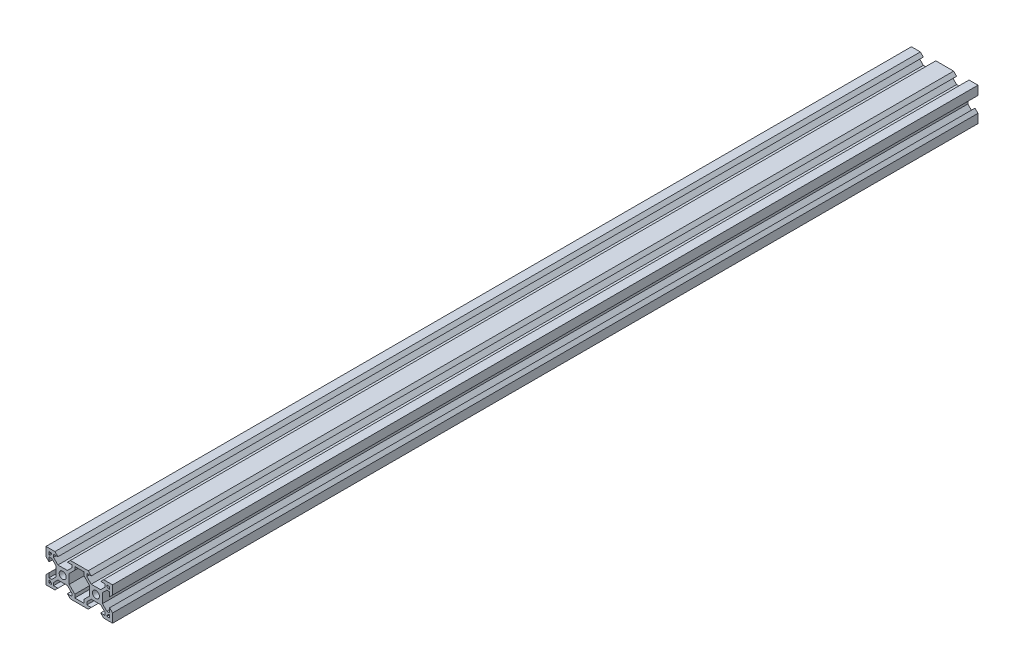
SolidWorks part; units mm, degrees
ref_plane "Front Plane" through (0, 0, 0) normal (0, 0, 1) x (1, 0, 0)
ref_plane "Top Plane" through (0, 0, 0) normal (0, 1, 0) x (1, 0, 0)
ref_plane "Right Plane" through (0, 0, 0) normal (1, 0, 0) x (0, 0, -1)
sketch "Sketch1" plane through (0, 0, 0) normal (0, 0, 1) x (1, 0, 0)
  line L0 (0, 0) -> (0, 5.36)
  line L1 (0, 20) -> (5.36, 20)
  line L3 (20, 0) -> (14.64, 0)
  line L4 (0, 10) -> (20, 10) construction
  line L5 (5.36, 0) -> (0, 0)
  line L6 (4.5007, 18.2) -> (7.16, 18.2)
  line L7 (17.3007, 3.76) -> (17.3007, 1.8)
  line L8 (15.4993, 1.8) -> (12.84, 1.8)
  line L9 (20, 0) -> (0, 0) construction
  line L10 (7.16, 1.8) -> (4.5007, 1.8)
  line L11 (15.4993, 3.44) -> (12.84, 6.0993)
  line L12 (4.5007, 16.56) -> (7.16, 13.9007)
  line L13 (13.9007, 12.84) -> (13.9007, 7.16)
  line L14 (12.84, 13.9007) -> (7.16, 13.9007)
  line L15 (6.0993, 12.84) -> (6.0993, 7.16)
  line L16 (7.16, 6.0993) -> (12.84, 6.0993)
  line L17 (4.5007, 16.56) -> (4.5007, 18.2)
  line L18 (3.44, 15.4993) -> (1.8, 15.4993)
  line L19 (4.5007, 3.44) -> (4.5007, 1.8)
  line L20 (3.44, 4.5007) -> (1.8, 4.5007)
  line L21 (15.4993, 3.44) -> (15.4993, 1.8)
  line L23 (17.3007, 1.8) -> (22.7007, 1.8)
  line L24 (15.4993, 16.56) -> (15.4993, 18.2)
  line L25 (7.16, 18.2) -> (5.36, 20)
  line L26 (12.84, 1.8) -> (14.64, 0)
  line L27 (7.16, 1.8) -> (5.36, 0)
  line L28 (12.84, 18.2) -> (14.64, 20)
  line L29 (1.8, 7.16) -> (0, 5.36)
  line L30 (1.8, 12.84) -> (0, 14.64)
  line L31 (22.7007, 1.8) -> (22.7007, 3.76)
  line L32 (17.3007, 16.24) -> (17.3007, 18.2)
  line L33 (17.3007, 18.2) -> (22.6993, 18.2)
  line L34 (22.6993, 18.2) -> (22.6993, 16.24)
  line L35 (38.2013, 12.8423) -> (40.001, 14.6427)
  line L36 (38.2024, 7.1623) -> (40.0028, 5.3627)
  line L37 (27.16, 18.2) -> (25.36, 20)
  line L38 (32.84, 1.8) -> (34.64, 0)
  line L39 (27.16, 1.8) -> (25.36, 0)
  line L40 (32.84, 18.2) -> (34.64, 20)
  line L41 (24.5013, 16.5597) -> (24.5009, 18.2)
  line L42 (1.8, 18.2) -> (3.4307, 18.2)
  line L43 (3.4307, 18.2) -> (3.4307, 17.63)
  line L44 (24.5038, 3.4397) -> (24.5041, 1.8)
  line L45 (36.5629, 4.5027) -> (38.2029, 4.503)
  line L46 (35.5025, 3.4418) -> (35.5028, 1.8)
  line L47 (36.5608, 15.5014) -> (38.2008, 15.5017)
  line L48 (35.4999, 16.5618) -> (35.4996, 18.2)
  line L49 (32.8426, 6.1006) -> (27.1626, 6.0995)
  line L50 (33.902, 12.8415) -> (33.9031, 7.1615)
  line L51 (27.1611, 13.9009) -> (32.8411, 13.902)
  line L52 (26.1007, 12.84) -> (26.1007, 7.16)
  line L53 (1.8, 4.5007) -> (1.8, 7.16)
  line L54 (24.5038, 3.4397) -> (27.1626, 6.0995)
  line L55 (35.5025, 3.4418) -> (32.8426, 6.1006)
  line L56 (36.5629, 4.5027) -> (33.9031, 7.1615)
  line L57 (24.5041, 1.8) -> (27.16, 1.8)
  line L58 (3.4307, 17.63) -> (2.37, 16.5693)
  line L59 (3.44, 4.5007) -> (6.0993, 7.16)
  line L60 (35.4996, 18.2) -> (32.84, 18.2)
  line L61 (20, 0) -> (25.36, 0)
  line L62 (39.9999, 20) -> (34.64, 20)
  line L63 (40.0038, 0) -> (40.0028, 5.3627)
  line L64 (1.8, 12.84) -> (1.8, 15.4993)
  line L65 (1.8, 1.8) -> (1.8, 18.2) construction
  line L66 (0, 14.64) -> (0, 20)
  line L67 (0, 0) -> (0, 20) construction
  line L68 (14.64, 20) -> (20, 20)
  line L69 (0, 20) -> (20, 20) construction
  line L70 (12.84, 18.2) -> (15.4993, 18.2)
  line L71 (1.8, 18.2) -> (18.2, 18.2) construction
  line L72 (25.36, 20) -> (20, 20)
  line L73 (27.16, 18.2) -> (24.5009, 18.2)
  line L74 (38.2013, 12.8423) -> (38.2008, 15.5017)
  line L75 (40.001, 14.6427) -> (39.9999, 20)
  line L76 (32.84, 1.8) -> (35.5028, 1.8)
  line L77 (34.64, 0) -> (40.0038, 0)
  line L78 (38.2029, 4.503) -> (38.2024, 7.1623)
  line L79 (35.4999, 16.5618) -> (32.8411, 13.902)
  line L80 (4.5007, 3.44) -> (7.16, 6.0993)
  line L81 (2.37, 16.5693) -> (1.8, 16.5693)
  line L82 (18.2, 1.8) -> (1.8, 1.8) construction
  line L83 (18.2, 18.2) -> (18.2, 1.8) construction
  line L84 (1.8, 16.5693) -> (1.8, 18.2)
  line L85 (20, 20) -> (20, 0) construction
  line L86 (1.8, 3.4307) -> (1.8, 1.8)
  line L87 (2.37, 3.4307) -> (1.8, 3.4307)
  line L88 (3.4307, 2.37) -> (2.37, 3.4307)
  line L89 (3.4307, 1.8) -> (3.4307, 2.37)
  line L90 (1.8, 1.8) -> (3.4307, 1.8)
  line L91 (13.9007, 7.16) -> (17.3007, 3.76)
  line L92 (20, 20) -> (20, -0.3542) construction
  line L93 (38.2, 1.8) -> (36.5693, 1.8)
  line L94 (36.5693, 1.8) -> (36.5693, 2.37)
  line L95 (36.5693, 2.37) -> (37.63, 3.4307)
  line L96 (37.63, 3.4307) -> (38.2, 3.4307)
  line L97 (38.2, 3.4307) -> (38.2, 1.8)
  line L98 (38.2, 16.5693) -> (38.2, 18.2)
  line L99 (37.63, 16.5693) -> (38.2, 16.5693)
  line L100 (36.5693, 17.63) -> (37.63, 16.5693)
  line L101 (36.5693, 18.2) -> (36.5693, 17.63)
  line L102 (38.2, 18.2) -> (36.5693, 18.2)
  line L103 (6.0993, 12.84) -> (3.44, 15.4993)
  line L104 (13.9007, 12.84) -> (17.3007, 16.24)
  line L105 (12.84, 13.9007) -> (15.4993, 16.56)
  line L106 (33.902, 12.8415) -> (36.5608, 15.5014)
  line L108 (27.1611, 13.9009) -> (24.5013, 16.5597)
  line L109 (26.1007, 12.84) -> (22.6993, 16.24)
  line L110 (26.1007, 7.16) -> (22.7007, 3.76)
  circle A0 centre (10, 10) radius 2.1
  circle A1 centre (30, 10) radius 2.1
  point P14 (17.3007, 3.76)
  point P81 (0, 0)
  point P82 (0, 0)
  point P112 (17.3007, 1.8)
  dimension "D3" = 4.2
  dimension "D1" = 20
  dimension "D2" = 20
  dimension "D5" = 5.4
  dimension "D7" = 1.07
  dimension "D8" = 45
  dimension "D9" = 1.5
  dimension "D10" = 4.5007
  dimension "D11" = 5.68
  dimension "D12" = 5.68
  dimension "D13" = 5.68
  dimension "D14" = 5.68
  dimension "D15" = 1.64
  dimension "D16" = 1.64
  dimension "D17" = 1.64
  dimension "D18" = 1.64
  dimension "D19" = 1.64
  dimension "D20" = 15.4993
  dimension "D21" = 1.07
  dimension "D22" = 1.64
  dimension "D23" = 45
  dimension "D24" = 45
  dimension "D25" = 1.5
  dimension "D26" = 45
  dimension "D27" = 45
  dimension "D28" = 45
  dimension "D4" = 1.8
extrude "Boss-Extrude1" add sketch "Sketch1" against normal blind 520
